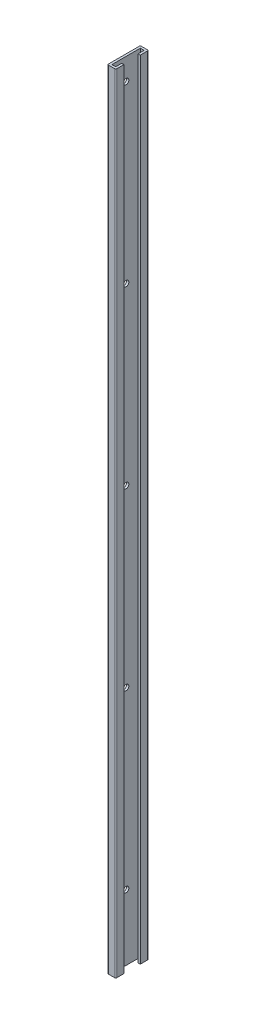
SolidWorks part; units mm, degrees
ref_plane "Front" through (0, 0, 0) normal (0, 0, 1) x (1, 0, 0)
ref_plane "Top" through (0, 0, 0) normal (0, 1, 0) x (1, 0, 0)
ref_plane "Right" through (0, 0, 0) normal (1, 0, 0) x (0, 0, -1)
sketch "Sketch1" plane through (0, 0, 0) normal (0, 1, 0) x (1, 0, 0)
  line L0 (9.525, 34.29) -> (9.525, 26.035)
  line L1 (1.27, -2.54) -> (8.255, -2.54)
  line L2 (0, -1.27) -> (0, 34.29)
  line L3 (1.27, 35.56) -> (8.255, 35.56)
  line L5 (9.525, -1.27) -> (9.525, 6.985)
  line L6 (6.985, 0) -> (6.985, 6.985)
  line L7 (2.54, 0) -> (6.985, 0)
  line L8 (2.54, 0) -> (2.54, 33.02)
  line L9 (2.54, 33.02) -> (6.985, 33.02)
  line L10 (6.985, 33.02) -> (6.985, 26.035)
  line L11 (9.525, 6.985) -> (6.985, 6.985)
  line L12 (9.525, 26.035) -> (6.985, 26.035)
  line L13 (0, -2.54) -> (0, 35.56) construction
  line L14 (0, 35.56) -> (9.525, 35.56) construction
  line L15 (0, -2.54) -> (9.525, -2.54) construction
  line L16 (9.525, -2.54) -> (9.525, 6.985) construction
  line L17 (9.525, 35.56) -> (9.525, 26.035) construction
  arc A0 (0, 34.29) -> (1.27, 35.56) centre (1.27, 34.29) cw
  arc A1 (1.27, -2.54) -> (0, -1.27) centre (1.27, -1.27) cw
  arc A2 (8.255, -2.54) -> (9.525, -1.27) centre (8.255, -1.27) ccw
  arc A3 (8.255, 35.56) -> (9.525, 34.29) centre (8.255, 34.29) cw
  point P16 (0, 35.56)
  dimension "D5" = 1.27
  dimension "D1" = 38.1
  dimension "D2" = 9.525
  dimension "D3" = 9.525
  dimension "D4" = 2.54
extrude "Boss-Extrude1" add sketch "Sketch1" along normal blind 914.4
sketch "Sketch2" plane through (2.54, 0, 0) normal (1, 0, 0) x (0, 0, -1)
  line L0 (16.51, 76.2) -> (16.51, 0) construction
  line L1 (34.29, 0) -> (-1.27, 0) construction
  circle A0 centre (16.51, 76.2) radius 3.175
  circle A1 centre (16.51, 279.4) radius 3.175
  circle A2 centre (16.51, 482.6) radius 3.175
  circle A3 centre (16.51, 685.8) radius 3.175
  circle A4 centre (16.51, 889) radius 3.175
  dimension "D1" = 6.35
  dimension "D2" = 76.2
  dimension "D3" = 5
extrude "Cut-Extrude1" cut sketch "Sketch2" against normal up to next
